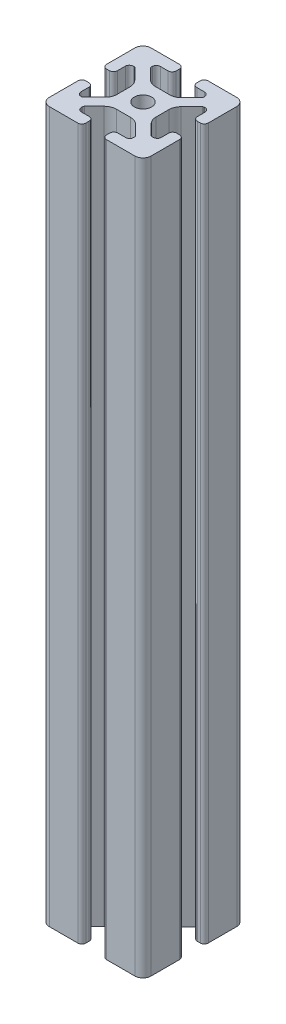
SolidWorks part; units mm, degrees
ref_plane "Front Plane" through (0, 0, 0) normal (0, 0, 1) x (1, 0, 0)
ref_plane "Top Plane" through (0, 0, 0) normal (0, 1, 0) x (1, 0, 0)
ref_plane "Right Plane" through (0, 0, 0) normal (1, 0, 0) x (0, 0, -1)
sketch "Sketch2" plane through (0, 0, 0) normal (0, 0, 1) x (1, 0, 0)
  line L0 (0, 0) -> (0, 279.4)
  dimension "D1" = 279.4
other "40 series 4040(1)"
ref_plane "Plane1" through (0, 0, 0) normal (0, 1, 0) x (-1, 0, 0)
sketch "Sketch12" plane through (0, 0, 0) normal (0, 1, 0) x (-1, 0, 0)
  line L88 (-5.63, -15.5246) -> (-8.715, -15.5246)
  line L89 (-10.285, -13.9546) -> (-10.285, -13.4925)
  line L90 (-10.0624, -12.9551) -> (-6.2171, -9.1098)
  line L91 (-2.7773, -7.685) -> (2.7773, -7.685)
  line L92 (6.2171, -9.1098) -> (10.0624, -12.9551)
  line L93 (10.285, -13.4925) -> (10.285, -13.9546)
  line L94 (8.715, -15.5246) -> (5.63, -15.5246)
  line L95 (4.06, -17.0946) -> (4.06, -18.43)
  line L96 (5.63, -20) -> (16.83, -20)
  line L97 (20, -16.83) -> (20, -5.63)
  line L98 (18.43, -4.06) -> (17.25, -4.06)
  line L99 (15.68, -5.63) -> (15.68, -8.7154)
  line L100 (14.11, -10.2854) -> (13.6201, -10.2854)
  line L101 (13.1637, -9.947) -> (9.0762, -5.8595)
  line L102 (7.685, -2.5008) -> (7.685, 2.5008)
  line L103 (9.0762, 5.8595) -> (13.2795, 10.0628)
  line L104 (13.8169, 10.2854) -> (14.11, 10.2854)
  line L105 (15.68, 8.7154) -> (15.68, 5.63)
  line L106 (17.25, 4.06) -> (18.43, 4.06)
  line L107 (20, 5.63) -> (20, 16.83)
  line L108 (16.83, 20) -> (5.63, 20)
  line L109 (4.06, 18.43) -> (4.06, 17.0946)
  line L110 (5.63, 15.5246) -> (8.715, 15.5246)
  line L111 (10.285, 13.9546) -> (10.285, 13.4925)
  line L112 (10.0624, 12.9551) -> (6.2171, 9.1098)
  line L113 (2.7773, 7.685) -> (-2.7773, 7.685)
  line L114 (-6.2171, 9.1098) -> (-10.0624, 12.9551)
  line L115 (-10.285, 13.4925) -> (-10.285, 13.9546)
  line L116 (-8.715, 15.5246) -> (-5.63, 15.5246)
  line L117 (-4.06, 17.0946) -> (-4.06, 18.43)
  line L118 (-5.63, 20) -> (-16.83, 20)
  line L119 (-20, 16.83) -> (-20, 5.573)
  line L120 (-18.43, 4.003) -> (-17.25, 4.003)
  line L121 (-15.68, 5.573) -> (-15.68, 8.4757)
  line L122 (-14.0552, 10.0447) -> (-13.7199, 10.033)
  line L123 (-13.0405, 9.8238) -> (-9.0762, 5.8595)
  line L124 (-7.685, 2.5008) -> (-7.685, -2.5008)
  line L125 (-9.0762, -5.8595) -> (-13.2795, -10.0628)
  line L126 (-13.8169, -10.2854) -> (-14.11, -10.2854)
  line L127 (-15.68, -8.7154) -> (-15.68, -5.7579)
  line L128 (-17.25, -4.1204) -> (-18.43, -4.1204)
  line L129 (-20, -5.7579) -> (-20, -17.0184)
  line L130 (-16.6746, -20) -> (-5.63, -20)
  line L131 (-4.06, -18.43) -> (-4.06, -17.0946)
  circle A1 centre (0, 0) radius 3.4
  arc A88 (-4.06, -17.0946) -> (-5.63, -15.5246) centre (-5.63, -17.0946) ccw
  arc A89 (-10.285, -13.9546) -> (-8.715, -15.5246) centre (-8.715, -13.9546) ccw
  arc A90 (-10.0624, -12.9551) -> (-10.285, -13.4925) centre (-9.525, -13.4925) ccw
  arc A91 (-2.7773, -7.685) -> (-6.2171, -9.1098) centre (-2.7773, -12.5496) ccw
  arc A92 (6.2171, -9.1098) -> (2.7773, -7.685) centre (2.7773, -12.5496) ccw
  arc A93 (10.285, -13.4925) -> (10.0624, -12.9551) centre (9.525, -13.4925) ccw
  arc A94 (8.715, -15.5246) -> (10.285, -13.9546) centre (8.715, -13.9546) ccw
  arc A95 (5.63, -15.5246) -> (4.06, -17.0946) centre (5.63, -17.0946) ccw
  arc A96 (4.06, -18.43) -> (5.63, -20) centre (5.63, -18.43) ccw
  arc A97 (16.83, -20) -> (20, -16.83) centre (16.83, -16.83) ccw
  arc A98 (20, -5.63) -> (18.43, -4.06) centre (18.43, -5.63) ccw
  arc A99 (17.25, -4.06) -> (15.68, -5.63) centre (17.25, -5.63) ccw
  arc A100 (14.11, -10.2854) -> (15.68, -8.7154) centre (14.11, -8.7154) ccw
  arc A101 (13.1637, -9.947) -> (13.6201, -10.2854) centre (13.8117, -9.55) ccw
  arc A102 (7.685, -2.5008) -> (9.0762, -5.8595) centre (12.435, -2.5008) ccw
  arc A103 (9.0762, 5.8595) -> (7.685, 2.5008) centre (12.435, 2.5008) ccw
  arc A104 (13.8169, 10.2854) -> (13.2795, 10.0628) centre (13.8169, 9.5254) ccw
  arc A105 (15.68, 8.7154) -> (14.11, 10.2854) centre (14.11, 8.7154) ccw
  arc A106 (15.68, 5.63) -> (17.25, 4.06) centre (17.25, 5.63) ccw
  arc A107 (18.43, 4.06) -> (20, 5.63) centre (18.43, 5.63) ccw
  arc A108 (20, 16.83) -> (16.83, 20) centre (16.83, 16.83) ccw
  arc A109 (5.63, 20) -> (4.06, 18.43) centre (5.63, 18.43) ccw
  arc A110 (4.06, 17.0946) -> (5.63, 15.5246) centre (5.63, 17.0946) ccw
  arc A111 (10.285, 13.9546) -> (8.715, 15.5246) centre (8.715, 13.9546) ccw
  arc A112 (10.0624, 12.9551) -> (10.285, 13.4925) centre (9.525, 13.4925) ccw
  arc A113 (2.7773, 7.685) -> (6.2171, 9.1098) centre (2.7773, 12.5496) ccw
  arc A114 (-6.2171, 9.1098) -> (-2.7773, 7.685) centre (-2.7773, 12.5496) ccw
  arc A115 (-10.285, 13.4925) -> (-10.0624, 12.9551) centre (-9.525, 13.4925) ccw
  arc A116 (-8.715, 15.5246) -> (-10.285, 13.9546) centre (-8.715, 13.9546) ccw
  arc A117 (-5.63, 15.5246) -> (-4.06, 17.0946) centre (-5.63, 17.0946) ccw
  arc A118 (-4.06, 18.43) -> (-5.63, 20) centre (-5.63, 18.43) ccw
  arc A119 (-16.83, 20) -> (-20, 16.83) centre (-16.83, 16.83) ccw
  arc A120 (-20, 5.573) -> (-18.43, 4.003) centre (-18.43, 5.573) ccw
  arc A121 (-17.25, 4.003) -> (-15.68, 5.573) centre (-17.25, 5.573) ccw
  arc A122 (-14.0552, 10.0447) -> (-15.68, 8.4757) centre (-14.11, 8.4757) ccw
  arc A123 (-13.0405, 9.8238) -> (-13.7199, 10.033) centre (-13.5779, 9.2864) ccw
  arc A124 (-7.685, 2.5008) -> (-9.0762, 5.8595) centre (-12.435, 2.5008) ccw
  arc A125 (-9.0762, -5.8595) -> (-7.685, -2.5008) centre (-12.435, -2.5008) ccw
  arc A126 (-13.8169, -10.2854) -> (-13.2795, -10.0628) centre (-13.8169, -9.5254) ccw
  arc A127 (-15.68, -8.7154) -> (-14.11, -10.2854) centre (-14.11, -8.7154) ccw
  arc A128 (-15.68, -5.7579) -> (-17.25, -4.1204) centre (-17.2485, -5.6904) ccw
  arc A129 (-18.43, -4.1204) -> (-20, -5.7579) centre (-18.4315, -5.6904) ccw
  arc A130 (-20, -17.0184) -> (-16.6746, -20) centre (-16.8354, -16.8341) ccw
  arc A131 (-5.63, -20) -> (-4.06, -18.43) centre (-5.63, -18.43) ccw
  point P5 (0, 20)
  point P15 (-20, 20)
  point P20 (20, 20)
  point P25 (20, 0)
  point P30 (20, -20)
  point P35 (0, -20)
  point P40 (-20, -20)
  point P45 (-20, 0)
  point P50 (0, 0)
  point P55 (0, 0)
